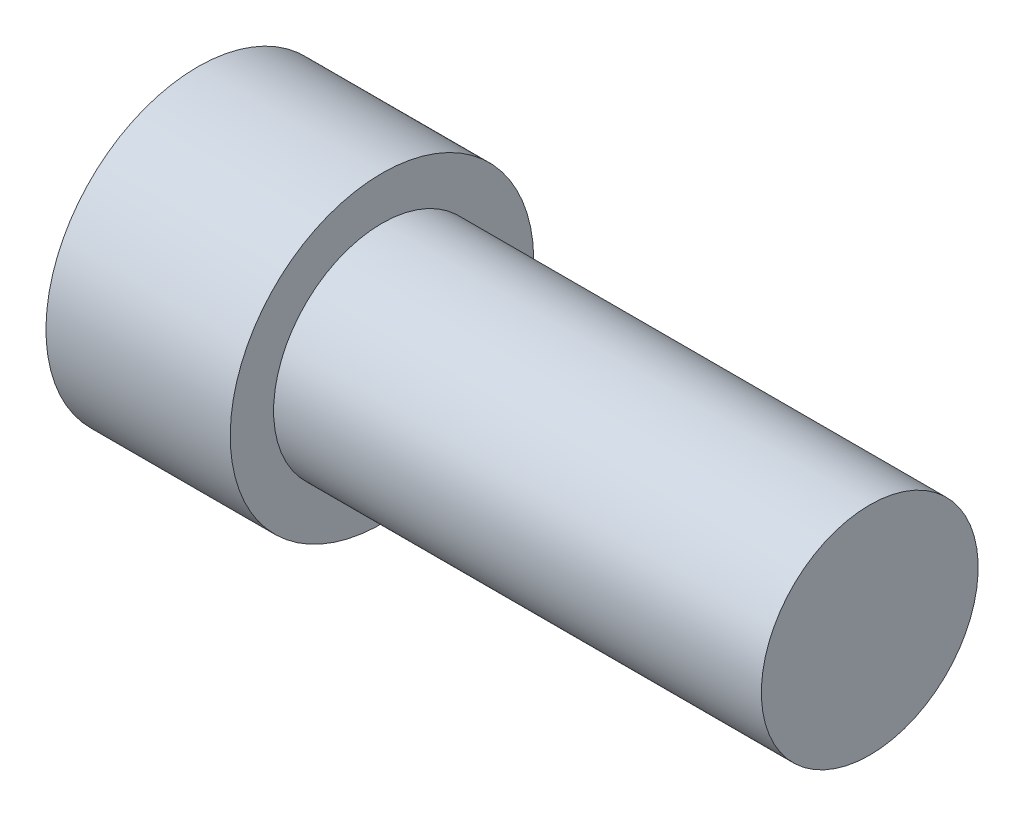
SolidWorks part; units mm, degrees
ref_plane "Front Plane" through (0, 0, 0) normal (0, 0, 1) x (1, 0, 0)
ref_plane "Top Plane" through (0, 0, 0) normal (0, 1, 0) x (1, 0, 0)
ref_plane "Right Plane" through (0, 0, 0) normal (1, 0, 0) x (0, 0, -1)
sketch "Sketch1" plane through (0, 0, 0) normal (0, 0, 1) x (1, 0, 0)
  line L0 (-31, 0.2864) -> (-31, 14.2864)
  line L1 (-31, 14.2864) -> (-14, 14.2864)
  line L2 (-14, 14.2864) -> (-14, 10.2864)
  line L3 (-14, 10.2864) -> (31, 10.2864)
  line L4 (31, 10.2864) -> (31, 0.2864)
  line L5 (31, 0.2864) -> (-31, 0.2864)
  point P2 (-14, 14.2864)
  dimension "D1" = 14
  dimension "D2" = 10
  dimension "D3" = 17
  dimension "D4" = 45
  dimension "D5" = 31
  dimension "D6" = 14.2864
revolve "Revolve1" add sketch "Sketch1" angle 360 about L5
sketch "Sketch2" plane through (-31, 0, 0) normal (-1, 0, 0) x (0, 0, 1)
  line L1 (11.547, 0) -> (5.7735, 10)
  line L2 (5.7735, 10) -> (-5.7735, 10)
  line L3 (-5.7735, 10) -> (-11.547, 0)
  line L4 (-11.547, 0) -> (-5.7735, -10)
  line L5 (-5.7735, -10) -> (5.7735, -10)
  line L6 (5.7735, -10) -> (11.547, 0)
  circle A0 centre (0, 0) radius 10 construction
  point P1 (0, 0)
  dimension "D1" = 20
extrude "Cut-Extrude1" cut sketch "Sketch2" against normal blind 10
